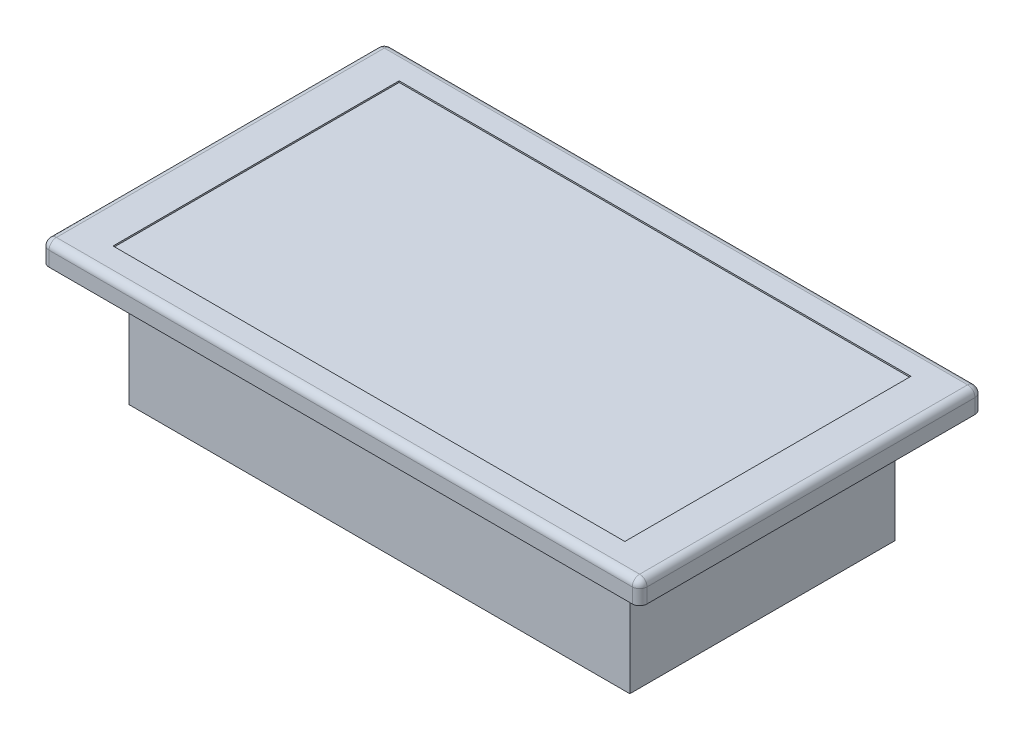
SolidWorks part; units mm, degrees
material "6061-T6 (SS)"
ref_plane "Front Plane" through (0, 0, 0) normal (0, 0, 1) x (1, 0, 0)
ref_plane "Top Plane" through (0, 0, 0) normal (0, 1, 0) x (1, 0, 0)
ref_plane "Right Plane" through (0, 0, 0) normal (1, 0, 0) x (0, 0, -1)
sketch "Sketch1" plane through (0, 0, 0) normal (0, 1, 0) x (1, 0, 0)
  line L1 (-43.18, -22.86) -> (43.18, -22.86)
  line L2 (-43.18, -22.86) -> (-43.18, 22.86)
  line L3 (-43.18, 22.86) -> (43.18, 22.86)
  line L4 (43.18, -22.86) -> (43.18, 22.86)
  line L5 (0, 22.86) -> (0, -22.86) construction
  line L6 (-43.18, 0) -> (43.18, 0) construction
  point P0 (0, 0)
  dimension "D1" = 45.72
  dimension "D2" = 86.36
extrude "Boss-Extrude1" add sketch "Sketch1" along normal blind 20.32
sketch "Sketch2" plane through (0, 0, 0) normal (0, -1, 0) x (1, 0, 0)
  line L0 (-43.18, -22.86) -> (-43.18, 22.86) construction
  line L1 (-43.18, 12.4702) -> (-29.9886, 12.4702)
  line L2 (-43.18, 12.4702) -> (-43.18, -13.3411)
  line L3 (-43.18, -13.3411) -> (-29.9886, -13.3411)
  line L4 (-29.9886, 12.4702) -> (-29.9886, -13.3411)
extrude "Cut-Extrude1" cut sketch "Sketch2" against normal blind 15.494
sketch "Sketch3" plane through (0, 20.32, 0) normal (0, 1, 0) x (1, 0, 0)
  line L1 (-51.5655, -29.5498) -> (51.5655, -29.5498)
  line L2 (-51.5655, -29.5498) -> (-51.5655, 29.5498)
  line L3 (-51.5655, 29.5498) -> (51.5655, 29.5498)
  line L4 (51.5655, -29.5498) -> (51.5655, 29.5498)
  line L5 (0, 29.5498) -> (0, -29.5498) construction
  line L6 (-51.5655, 0) -> (51.5655, 0) construction
  point P0 (0, 0)
extrude "Boss-Extrude2" add sketch "Sketch3" along normal blind 3.81
fillet "Fillet1" radius 1.27 4 edges at (-51.5655, 22.225, -29.5498) (51.5655, 22.225, -29.5498) (51.5655, 22.225, 29.5498) (-51.5655, 22.225, 29.5498)
fillet "Fillet2" radius 1.27 8 edges at (51.1936, 24.13, -29.1778) (51.5655, 24.13, 0) (51.1936, 24.13, 29.1778) (0, 24.13, 29.5498) (-51.1936, 24.13, 29.1778) (-51.5655, 24.13, 0) (-51.1936, 24.13, -29.1778) (0, 24.13, -29.5498)
sketch "Sketch4" plane through (0, 24.13, 0) normal (0, 1, 0) x (1, 0, 0)
  line L1 (-44.1356, -24.6731) -> (44.1356, -24.6731)
  line L2 (-44.1356, -24.6731) -> (-44.1356, 24.6731)
  line L3 (-44.1356, 24.6731) -> (44.1356, 24.6731)
  line L4 (44.1356, -24.6731) -> (44.1356, 24.6731)
  line L5 (0, 24.6731) -> (0, -24.6731) construction
  line L6 (-44.1356, 0) -> (44.1356, 0) construction
  point P0 (0, 0)
extrude "Cut-Extrude2" cut sketch "Sketch4" against normal blind 0.254
